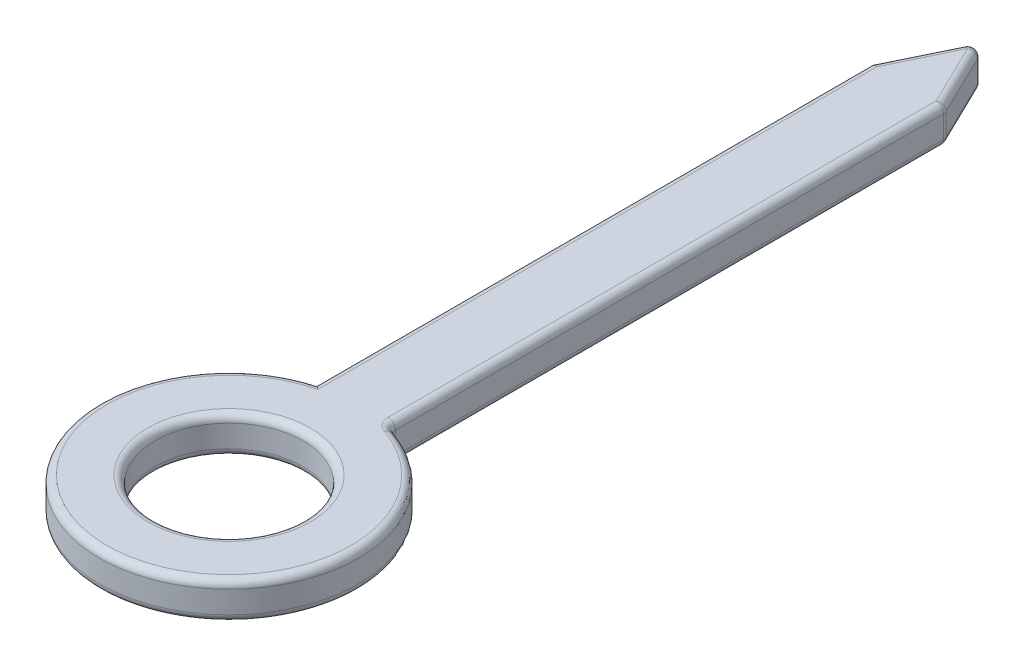
SolidWorks part; units mm, degrees
ref_plane "Front Plane" through (0, 0, 0) normal (0, 0, 1) x (1, 0, 0)
ref_plane "Top Plane" through (0, 0, 0) normal (0, 1, 0) x (1, 0, 0)
ref_plane "Right Plane" through (0, 0, 0) normal (1, 0, 0) x (0, 0, -1)
sketch "Sketch1" plane through (0, 0, 0) normal (0, 1, 0) x (1, 0, 0)
  line L1 (-0.127, 2.331) -> (0, 2.5927)
  line L2 (-0.127, 0.426) -> (-0.127, 2.331)
  line L4 (0.127, 0.426) -> (0.127, 2.331)
  line L5 (0, 2.5927) -> (0.127, 2.331)
  circle A0 centre (0, 0) radius 0.254
  arc A1 (-0.127, 0.426) -> (0.127, 0.426) centre (0, 0) ccw
  point P8 (0, 1.3785)
  dimension "D1" = 0.508
  dimension "D2" = 0.889
  dimension "D3" = 0.254
  dimension "D4" = 1.905
extrude "Extrude1" add sketch "Sketch1" along normal blind 0.127
fillet "Fillet1" radius 0.0254 15 edges at (-0.127, 0.127, -1.3785) (-0.0635, 0.127, -2.4619) (0.0635, 0.127, -2.4619) (0, 0.127, 0.4445) (0, 0.127, 0.254) (0.127, 0.0635, -0.426) (0.127, 0.127, -1.3785) (0.127, 0.0635, -2.331) (0, 0, 0.254) (0.127, 0, -1.3785) (0.0635, 0, -2.4619) (-0.0635, 0, -2.4619) (-0.127, 0, -1.3785) (0, 0, 0.4445) (0, 0.0635, -2.5927)
